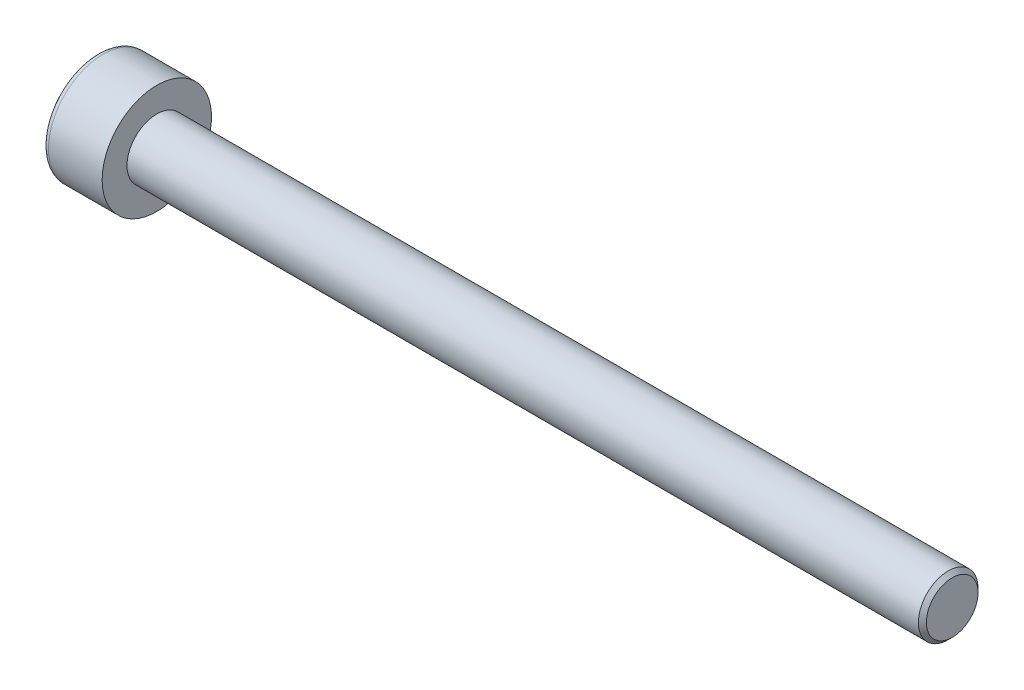
SolidWorks part; units mm, degrees
ref_plane "Vorne" through (0, 0, 0) normal (0, 0, 1) x (1, 0, 0)
ref_plane "Oben" through (0, 0, 0) normal (0, 1, 0) x (1, 0, 0)
ref_plane "Rechts" through (0, 0, 0) normal (1, 0, 0) x (0, 0, -1)
sketch "Skizze1" plane through (0, 0, 0) normal (0, 0, 1) x (1, 0, 0)
  line L0 (0, 0) -> (64.458, 0) construction
  line L1 (0, 0) -> (0, 2.45)
  line L2 (0.3, 2.75) -> (3, 2.75)
  line L3 (3, 2.75) -> (3, 1.5)
  line L4 (3, 1.5) -> (42.8, 1.5)
  line L5 (42.8, 1.5) -> (43, 1.3)
  line L6 (43, 1.3) -> (43, 0)
  line L7 (43, 0) -> (0, 0)
  arc A0 (0, 2.45) -> (0.3, 2.75) centre (0.3, 2.45) cw
  point P11 (0, 2.75)
  dimension "D7" = 0.3
  dimension "D1" = 3
  dimension "D2" = 45
  dimension "D3" = 0.2
  dimension "D4" = 5.5
  dimension "D5" = 3
  dimension "D6" = 40
revolve "Rotation1" add sketch "Skizze1" angle 360 about L0
cosmetic thread "Gewindedarstellung1" parameters "D1"=18, "D2"=2.439
sketch "Skizze2" plane through (0, 0, 0) normal (-1, 0, 0) x (0, 0, 1)
  line L1 (1.4434, 0) -> (0.7217, 1.25)
  line L2 (0.7217, 1.25) -> (-0.7217, 1.25)
  line L3 (-0.7217, 1.25) -> (-1.4434, 0)
  line L4 (-1.4434, 0) -> (-0.7217, -1.25)
  line L5 (-0.7217, -1.25) -> (0.7217, -1.25)
  line L6 (0.7217, -1.25) -> (1.4434, 0)
  circle A0 centre (0, 0) radius 1.25 construction
  dimension "D1" = 2.5
extrude "Schnitt-Linear austragen1" cut sketch "Skizze2" against normal blind 1.5
